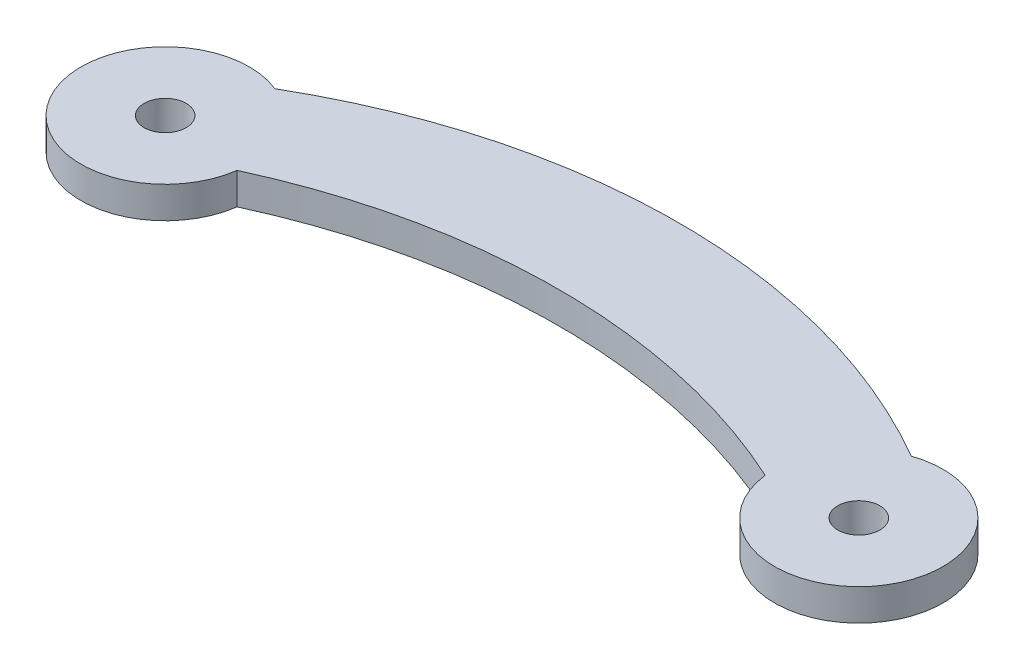
SolidWorks part; units mm, degrees
ref_plane "Front Plane" through (0, 0, 0) normal (0, 0, 1) x (1, 0, 0)
ref_plane "Top Plane" through (0, 0, 0) normal (0, 1, 0) x (1, 0, 0)
ref_plane "Right Plane" through (0, 0, 0) normal (1, 0, 0) x (0, 0, -1)
sketch "Sketch1" plane through (0, 0, 0) normal (0, 1, 0) x (1, 0, 0)
  arc A0 (1.5065, 3.7055) -> (3.9623, -0.5481) centre (0, 0) ccw
  arc A1 (29.0277, -0.5481) -> (31.702, 3.7055) centre (33, -0.0781) ccw
  arc A2 (1.5065, 3.7055) -> (31.702, 3.7055) centre (16.6042, -22.2186) cw
  arc A3 (3.9623, -0.5481) -> (29.0277, -0.5481) centre (16.495, -27.8049) cw
  point P3 (0, 0)
  point P8 (0, 0)
  point P9 (0, 0)
  dimension "D1" = 4
  dimension "D2" = 4
extrude "Boss-Extrude1" add sketch "Sketch1" along normal blind 1.5
sketch "Sketch3" plane through (0, 1.5, 0) normal (0, 1, 0) x (1, 0, 0)
  circle A0 centre (33, -0.0781) radius 1
  circle A1 centre (0, 0) radius 1
  dimension "D1" = 2
  dimension "D2" = 2
extrude "Cut-Extrude1" cut sketch "Sketch3" against normal blind 11.5
